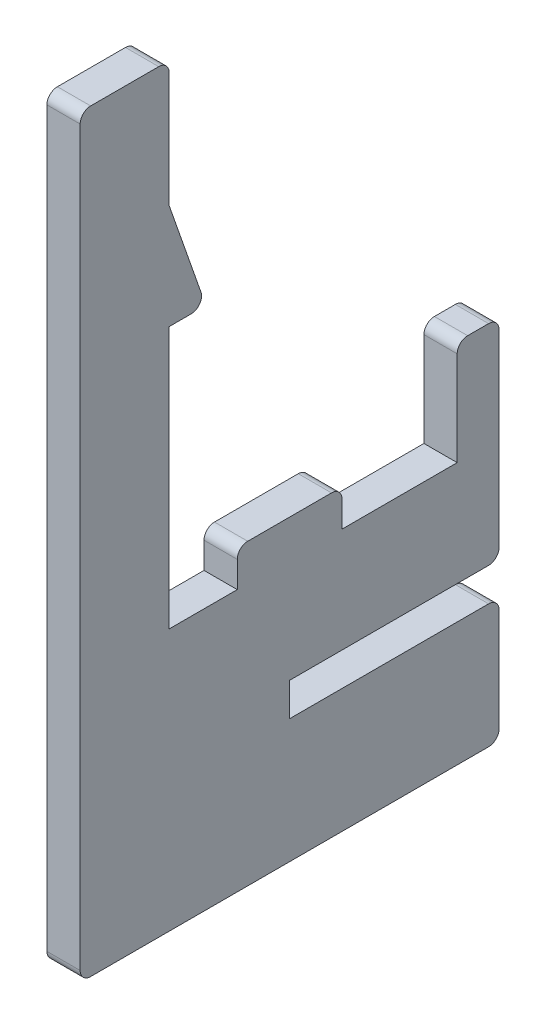
SolidWorks part; units mm, degrees
ref_plane "Front Plane" through (0, 0, 0) normal (0, 0, 1) x (1, 0, 0)
ref_plane "Top Plane" through (0, 0, 0) normal (0, 1, 0) x (1, 0, 0)
ref_plane "Right Plane" through (0, 0, 0) normal (1, 0, 0) x (0, 0, -1)
sketch "Sketch1" plane through (0, 0, 0) normal (1, 0, 0) x (0, 0, -1)
  line L0 (0, 0) -> (0, 25)
  line L1 (0, 0) -> (6.5, 0)
  line L2 (0, 25) -> (3.5, 25)
  line L3 (3.5, 25) -> (0, 35)
  line L4 (0, 35) -> (0, 47)
  line L5 (6.5, 0) -> (6.5, 3.5)
  line L6 (6.5, 3.5) -> (16.5, 3.5)
  line L7 (16.5, 3.5) -> (16.5, 0)
  line L8 (16.5, 0) -> (27.5, 0)
  line L9 (27.5, 0) -> (27.5, 10)
  line L10 (31.5, -10) -> (-8.5, -10)
  line L11 (27.5, 10) -> (31.5, 10)
  line L12 (31.5, 10) -> (31.5, -10)
  line L13 (0, 47) -> (-8.5, 47)
  line L14 (-8.5, 47) -> (-8.5, -10)
  line L15 (-8.5, -10) -> (-8.5, -25)
  line L16 (-8.5, -25) -> (31.5, -25)
  line L17 (31.5, -25) -> (31.5, -13.175)
  line L18 (31.5, -13.175) -> (11.5, -13.175)
  line L19 (11.5, -13.175) -> (11.5, -10)
  point P24 (11.5, -10)
  point P25 (11.5, 3.5)
  dimension "D12" = 25
  dimension "D13" = 15
  dimension "D14" = 3.175
  dimension "D2" = 6.5
  dimension "D3" = 3.5
  dimension "D4" = 10
  dimension "D5" = 12
  dimension "D6" = 10
  dimension "D7" = 3.5
  dimension "D8" = 11
  dimension "D9" = 10
  dimension "D10" = 40
  dimension "D11" = 10
extrude "Boss-Extrude1" add sketch "Sketch1" along normal blind 3.175 contours L13 L14 L10 L12 L11 L9 L8 L7 L6 L5 L1 L0 L2 L3 L4 | L18 L19 L10 L15 L16 L17
fillet "Fillet1" radius 1 11 edges at (1.5875, -25, 8.5) (1.5875, -25, -31.5) (1.5875, -13.175, -31.5) (1.5875, -10, -31.5) (1.5875, 3.5, -6.5) (1.5875, 3.5, -16.5) (1.5875, 47, 8.5) (1.5875, 47, 0) (1.5875, 10, -31.5) (1.5875, 10, -27.5) (1.5875, 25, -3.5)
